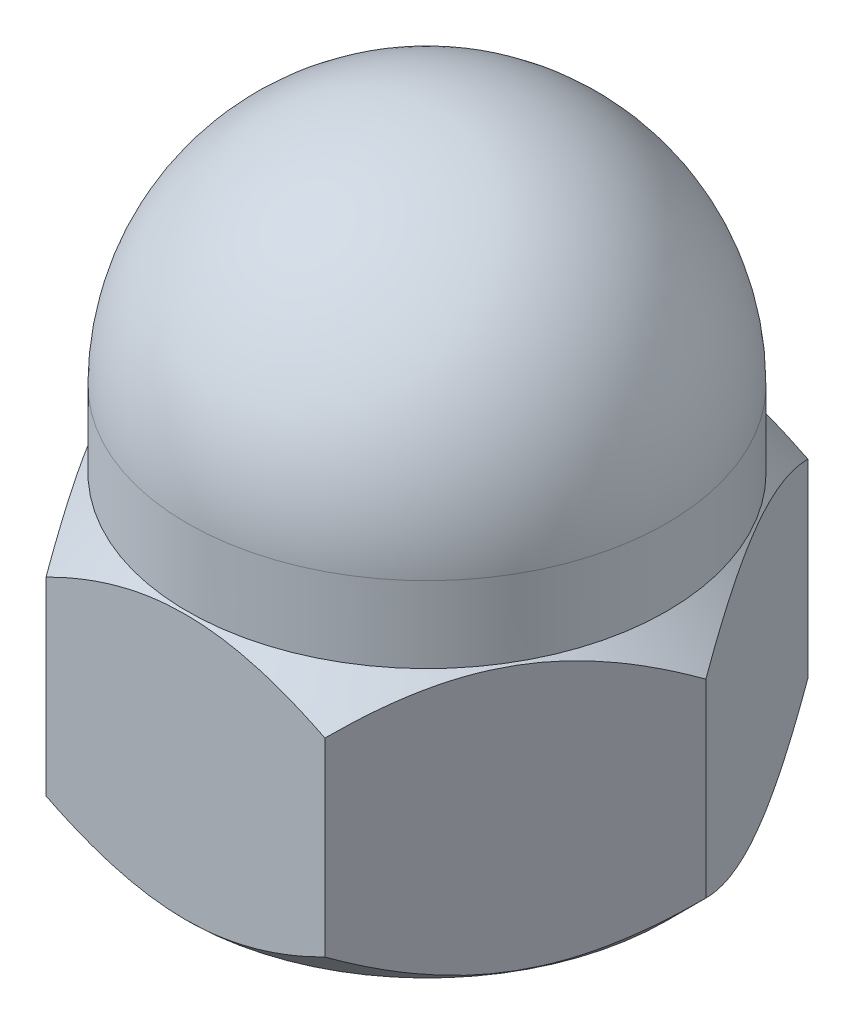
SolidWorks part; units mm, degrees
material "1023 Carbon Steel Sheet (SS)"
ref_plane "Front Plane" through (0, 0, 0) normal (0, 0, 1) x (1, 0, 0)
ref_plane "Top Plane" through (0, 0, 0) normal (0, 1, 0) x (1, 0, 0)
ref_plane "Right Plane" through (0, 0, 0) normal (1, 0, 0) x (0, 0, -1)
sketch "Sketch1" plane through (0, 0, 0) normal (0, 1, 0) x (1, 0, 0)
  line L1 (19.775, 0) -> (9.8875, 17.1257)
  line L2 (9.8875, 17.1257) -> (-9.8875, 17.1257)
  line L3 (-9.8875, 17.1257) -> (-19.775, 0)
  line L4 (-19.775, 0) -> (-9.8875, -17.1257)
  line L5 (-9.8875, -17.1257) -> (9.8875, -17.1257)
  line L6 (9.8875, -17.1257) -> (19.775, 0)
  circle A0 centre (0, 0) radius 17.1257 construction
  dimension "D1" = 39.55
extrude "Boss-Extrude1" add sketch "Sketch1" along normal blind 19 contours L2 L3 L4 L5 L6 L1
sketch "Sketch2" plane through (0, 0, 0) normal (-1, 0, 0) x (0, 0, 1)
  line L0 (-17, 24.4) -> (-17, 19)
  line L1 (0, -1000) -> (0, 49000) construction
  line L2 (-17.1257, 19) -> (0, 19) construction
  line L3 (-17, 19) -> (0, 19)
  line L4 (0, 19) -> (0, 41.4)
  arc A1 (0, 41.4) -> (-17, 24.4) centre (0, 24.4) ccw
  dimension "D1" = 41.4
  dimension "D2" = 17
revolve "Revolve1" add sketch "Sketch2" angle 360 about L1
hole_wizard "Ø20.0mm Dowel Hole1" positions "Sketch4" profile "Sketch5" hole size "Ø20.0" standard "ISO"
sketch "Sketch4" plane through (0, 0, 0) normal (0, -1, 0) x (-1, 0, 0)
  point P0 (0, 0)
sketch "Sketch5" plane through (0, 0, 0) normal (1, 0, 0) x (0, 0, -1)
  line L0 (0, 0) -> (0, 38.7103)
  line L1 (0, 38.7103) -> (12, 31.5)
  line L2 (12, 31.5) -> (12, 0)
  line L5 (12, 0) -> (0, 0)
  line L10 (0, 38.7103) -> (-12, 31.5) construction
  line L11 (0, -6.35) -> (0, 107.95) construction
  dimension "Hole Dia." = 24
  dimension "Hole Depth" = 31.5
  dimension "Drill Angle" = 118
sketch "Sketch6" plane through (0, 0, 0) normal (0, 0, 1) x (1, 0, 0)
  line L0 (17, 19) -> (17, 24.4) construction
  line L1 (17, 19) -> (17, 24.4) construction
  line L2 (19.775, 19) -> (17, 19)
  line L3 (17, 19) -> (19.775, 16.225)
  line L4 (19.775, 19) -> (19.775, 0) construction
  line L5 (19.775, 16.225) -> (19.775, 19)
  line L6 (-9.8875, 19) -> (-9.8875, 0) construction
  line L7 (-1009.8875, 9.5) -> (48990.1125, 9.5) construction
  line L8 (19.775, 2.775) -> (19.775, 0)
  line L9 (17, 0) -> (19.775, 2.775)
  line L10 (19.775, 0) -> (17, 0)
  line L11 (0, -1000) -> (0, 49000) construction
  point P3 (-9.8875, 9.5)
  dimension "D1" = 45
revolve "Cut-Revolve1" cut sketch "Sketch6" angle 360 about L11
